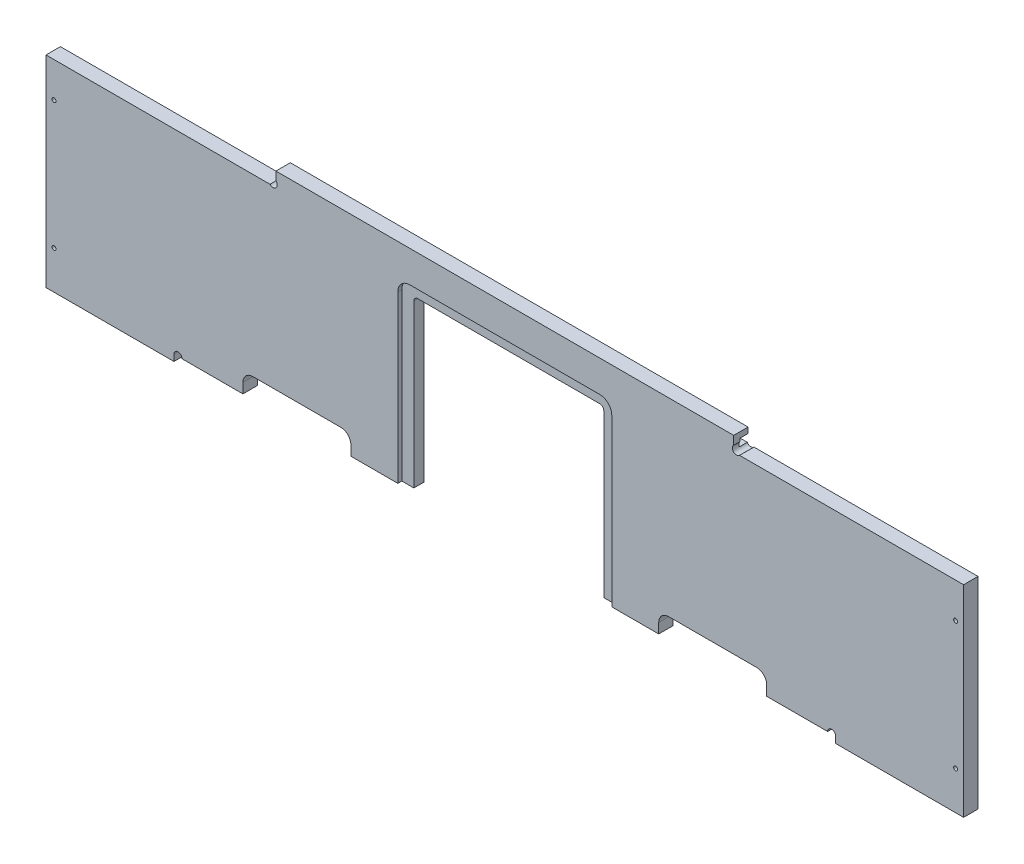
SolidWorks part; units mm, degrees
material "Pine"
ref_plane "Front Plane" through (0, 0, 0) normal (0, 0, 1) x (1, 0, 0)
ref_plane "Top Plane" through (0, 0, 0) normal (0, 1, 0) x (1, 0, 0)
ref_plane "Right Plane" through (0, 0, 0) normal (1, 0, 0) x (0, 0, -1)
sketch "Sketch1" plane through (0, 0, 0) normal (0, 0, 1) x (1, 0, 0)
  line L0 (-5300.6625, 1520.825) -> (-5451.475, 1520.825)
  line L1 (-5456.2375, 1384.3) -> (-5456.2375, 1516.0625)
  line L2 (-5557.8375, 1546.225) -> (-5194.3, 1546.225)
  line L3 (-5557.8375, 1539.875) -> (-5194.3, 1539.875)
  line L4 (-5297.4875, 1377.95) -> (-5454.65, 1377.95)
  line L5 (-5291.1375, 1384.3) -> (-5291.1375, 1516.0625)
  line L6 (-5300.6625, 1525.5875) -> (-5451.475, 1525.5875)
  line L7 (-5461, 1384.3) -> (-5461, 1516.0625)
  line L8 (-5297.4875, 1382.7125) -> (-5454.65, 1382.7125)
  line L9 (-5295.9, 1384.3) -> (-5295.9, 1516.0625)
  line L10 (-5740.4, 998.5375) -> (-5740.4, 1181.1)
  line L11 (-5740.4, 1181.1) -> (-5512.5938, 1181.1)
  line L12 (-5512.5938, 1181.1) -> (-5512.5938, 998.5375)
  line L13 (-5512.5938, 998.5375) -> (-5740.4, 998.5375)
  line L14 (-5258.5938, 1181.1) -> (-5486.4, 1181.1)
  line L15 (-5258.5938, 998.5375) -> (-5258.5938, 1181.1)
  line L16 (-5486.4, 998.5375) -> (-5258.5938, 998.5375)
  line L17 (-5486.4, 1181.1) -> (-5486.4, 998.5375)
  line L18 (-5740.4, 898.525) -> (-5011.7375, 898.525)
  line L19 (-5168.1062, 1384.3) -> (-5168.1062, 1392.2375)
  line L20 (-5176.0437, 1400.175) -> (-5245.8937, 1400.175)
  line L21 (-5253.8313, 1392.2375) -> (-5253.8313, 1384.3)
  line L22 (-5451.475, 1512.8875) -> (-5451.475, 1384.3)
  line L23 (-5303.8375, 1516.0625) -> (-5448.3, 1516.0625)
  line L24 (-5498.3062, 1384.3) -> (-5451.475, 1384.3)
  line L25 (-5253.8313, 1384.3) -> (-5300.6625, 1384.3)
  line L26 (-5584.0312, 1384.3) -> (-5740.4, 1384.3)
  line L27 (-5564.1875, 1536.7) -> (-5740.4, 1536.7)
  line L28 (-5740.4, 1357.3125) -> (-5740.4, 1206.5)
  line L29 (-5011.7375, 1357.3125) -> (-5740.4, 1357.3125)
  line L30 (-5011.7375, 1206.5) -> (-5011.7375, 1357.3125)
  line L31 (-5740.4, 1206.5) -> (-5011.7375, 1206.5)
  line L32 (-4765.675, 1549.4) -> (-4978.4, 1549.4)
  line L33 (-4765.675, 1397) -> (-4765.675, 1549.4)
  line L34 (-4978.4, 1397) -> (-4765.675, 1397)
  line L35 (-4978.4, 1549.4) -> (-4978.4, 1397)
  line L36 (-4765.675, 1371.6) -> (-4978.4, 1371.6)
  line L37 (-4765.675, 1219.2) -> (-4765.675, 1371.6)
  line L38 (-4978.4, 1219.2) -> (-4765.675, 1219.2)
  line L39 (-4978.4, 1371.6) -> (-4978.4, 1219.2)
  line L40 (-5284.7875, 803.275) -> (-5272.0875, 803.275)
  line L41 (-5187.95, 1536.7) -> (-5011.7375, 1536.7)
  line L42 (-5300.6625, 1384.3) -> (-5300.6625, 1512.8875)
  line L43 (-5740.4, 1536.7) -> (-5740.4, 1384.3)
  line L44 (-5557.8375, 1536.7) -> (-5557.8375, 1549.4)
  line L45 (-5557.8375, 1549.4) -> (-5194.3, 1549.4)
  line L46 (-5194.3, 1549.4) -> (-5194.3, 1536.7)
  line L47 (-5011.7375, 1536.7) -> (-5011.7375, 1384.3)
  line L48 (-5011.7375, 1384.3) -> (-5168.1062, 1384.3)
  line L49 (-5498.3062, 1384.3) -> (-5498.3062, 1392.2375)
  line L50 (-5506.2437, 1400.175) -> (-5576.0938, 1400.175)
  line L51 (-5584.0312, 1392.2375) -> (-5584.0312, 1384.3)
  line L52 (-5740.4, 660.4) -> (-5740.4, 898.525)
  line L53 (-5011.7375, 898.525) -> (-5011.7375, 660.4)
  line L54 (-5011.7375, 660.4) -> (-5740.4, 660.4)
  line L55 (-5291.1375, 803.275) -> (-5291.1375, 752.475)
  line L56 (-5265.7375, 752.475) -> (-5265.7375, 803.275)
  line L57 (-5284.7875, 752.475) -> (-5272.0875, 752.475)
  arc A0 (-5451.475, 1520.825) -> (-5456.2375, 1516.0625) centre (-5451.475, 1516.0625) ccw
  arc A1 (-5461, 1384.3) -> (-5454.65, 1377.95) centre (-5454.65, 1384.3) ccw
  arc A2 (-5297.4875, 1377.95) -> (-5291.1375, 1384.3) centre (-5297.4875, 1384.3) ccw
  circle A3 centre (-5037.9312, 1233.4875) radius 1.5875
  circle A4 centre (-5037.9312, 1328.7375) radius 1.5875
  circle A5 centre (-5714.2063, 1233.4875) radius 1.5875
  circle A6 centre (-5714.2063, 1328.7375) radius 1.5875
  circle A7 centre (-5018.0875, 1333.5) radius 1.5875
  circle A8 centre (-5018.0875, 1231.9) radius 1.5875
  circle A9 centre (-5734.05, 1231.9) radius 1.5875
  circle A10 centre (-5734.05, 1333.5) radius 1.5875
  circle A11 centre (-5734.05, 1511.3) radius 1.5875
  circle A12 centre (-5734.05, 1409.7) radius 1.5875
  circle A13 centre (-5018.0875, 1511.3) radius 1.5875
  circle A14 centre (-5018.0875, 1409.7) radius 1.5875
  arc A15 (-5557.8375, 1546.225) -> (-5557.8375, 1539.875) centre (-5557.8375, 1543.05) ccw
  arc A16 (-5194.3, 1539.875) -> (-5194.3, 1546.225) centre (-5194.3, 1543.05) ccw
  arc A17 (-5291.1375, 1516.0625) -> (-5300.6625, 1525.5875) centre (-5300.6625, 1516.0625) ccw
  arc A18 (-5451.475, 1525.5875) -> (-5461, 1516.0625) centre (-5451.475, 1516.0625) ccw
  arc A19 (-5456.2375, 1384.3) -> (-5454.65, 1382.7125) centre (-5454.65, 1384.3) ccw
  arc A20 (-5297.4875, 1382.7125) -> (-5295.9, 1384.3) centre (-5297.4875, 1384.3) ccw
  arc A21 (-5295.9, 1516.0625) -> (-5300.6625, 1520.825) centre (-5300.6625, 1516.0625) ccw
  circle A22 centre (-5702.3, 892.175) radius 1.5875
  circle A23 centre (-5734.05, 860.425) radius 1.5875
  circle A24 centre (-5474.8906, 892.175) radius 1.5875
  circle A25 centre (-5277.2469, 892.175) radius 1.5875
  circle A26 centre (-5049.8375, 892.175) radius 1.5875
  circle A27 centre (-5018.0875, 860.425) radius 1.5875
  circle A28 centre (-5296.6938, 1174.75) radius 1.5875
  circle A29 centre (-5448.3, 1174.75) radius 1.5875
  circle A30 centre (-5264.9437, 1155.7) radius 1.5875
  circle A31 centre (-5264.9437, 1023.9375) radius 1.5875
  circle A32 centre (-5518.9438, 1155.7) radius 1.5875
  circle A33 centre (-5518.9438, 1023.9375) radius 1.5875
  circle A34 centre (-5702.3, 1004.8875) radius 1.5875
  circle A35 centre (-5550.6937, 1004.8875) radius 1.5875
  arc A36 (-5576.0938, 1400.175) -> (-5584.0312, 1392.2375) centre (-5576.0938, 1392.2375) ccw
  arc A37 (-5168.1062, 1392.2375) -> (-5176.0437, 1400.175) centre (-5176.0437, 1392.2375) ccw
  arc A38 (-5245.8937, 1400.175) -> (-5253.8313, 1392.2375) centre (-5245.8937, 1392.2375) ccw
  arc A39 (-5448.3, 1516.0625) -> (-5451.475, 1512.8875) centre (-5448.3, 1512.8875) ccw
  arc A40 (-5284.7875, 803.275) -> (-5291.1375, 803.275) centre (-5287.9625, 803.275) ccw
  circle A41 centre (-5679.2812, 1026.3187) radius 1.5875
  circle A42 centre (-5679.2812, 1153.3187) radius 1.5875
  circle A43 centre (-5571.3313, 1153.3187) radius 1.5875
  circle A44 centre (-5571.3313, 1026.3187) radius 1.5875
  circle A45 centre (-5317.3312, 1153.3187) radius 1.5875
  circle A46 centre (-5317.3312, 1026.3187) radius 1.5875
  circle A47 centre (-5425.2812, 1026.3187) radius 1.5875
  circle A48 centre (-5425.2812, 1153.3187) radius 1.5875
  arc A49 (-5194.3, 1536.7) -> (-5187.95, 1536.7) centre (-5191.125, 1536.7) ccw
  arc A50 (-5564.1875, 1536.7) -> (-5557.8375, 1536.7) centre (-5561.0125, 1536.7) ccw
  arc A51 (-5300.6625, 1512.8875) -> (-5303.8375, 1516.0625) centre (-5303.8375, 1512.8875) ccw
  arc A52 (-5498.3062, 1392.2375) -> (-5506.2437, 1400.175) centre (-5506.2437, 1392.2375) ccw
  circle A53 centre (-5712.46, 784.225) radius 4.7625
  arc A54 (-5272.0875, 752.475) -> (-5265.7375, 752.475) centre (-5268.9125, 752.475) ccw
  arc A55 (-5291.1375, 752.475) -> (-5284.7875, 752.475) centre (-5287.9625, 752.475) ccw
  circle A56 centre (-5182.3938, 684.2125) radius 3.175
  circle A57 centre (-5239.5437, 684.2125) radius 3.175
  circle A58 centre (-5512.5938, 684.2125) radius 3.175
  circle A59 centre (-5569.7437, 684.2125) radius 3.175
  circle A60 centre (-5474.8906, 666.75) radius 1.5875
  circle A61 centre (-5277.2469, 666.75) radius 1.5875
  circle A62 centre (-5734.05, 698.5) radius 1.5875
  circle A63 centre (-5702.3, 666.75) radius 1.5875
  circle A64 centre (-5049.8375, 666.75) radius 1.5875
  circle A65 centre (-5018.0875, 698.5) radius 1.5875
  circle A66 centre (-5713.73, 835.025) radius 4.7625
  circle A67 centre (-5712.46, 819.785) radius 4.7625
  circle A68 centre (-5712.46, 802.005) radius 4.7625
  circle A69 centre (-5714.2063, 1314.45) radius 3.175
  circle A70 centre (-5037.9312, 1314.45) radius 3.175
  arc A71 (-5265.7375, 803.275) -> (-5272.0875, 803.275) centre (-5268.9125, 803.275) ccw
  ellipse E0 centre (-5371.3062, 1089.8188) end of major axis (-5277.6438, 1089.8188) minor radius 65.0875
  ellipse E1 centre (-5625.3062, 1089.8188) end of major axis (-5531.6438, 1089.8188) minor radius 65.0875
sketch "MainOutline" plane through (0, 0, 0) normal (0, 0, 1) x (1, 0, 0)
  line L0 (-5740.4, 1539.24) -> (-5740.4, 1384.3)
  line L1 (-5740.4, 1384.3) -> (-5584.0312, 1384.3)
  line L2 (-5584.0312, 1384.3) -> (-5584.0312, 1392.2375)
  line L3 (-5576.0938, 1400.175) -> (-5506.2437, 1400.175)
  line L4 (-5498.3062, 1392.2375) -> (-5498.3062, 1384.3)
  line L5 (-5498.3062, 1384.3) -> (-5451.475, 1384.3)
  line L6 (-5451.475, 1384.3) -> (-5451.475, 1512.8875)
  line L7 (-5448.3, 1516.0625) -> (-5303.8375, 1516.0625)
  line L8 (-5300.6625, 1512.8875) -> (-5300.6625, 1384.3)
  line L9 (-5300.6625, 1384.3) -> (-5253.8313, 1384.3)
  line L10 (-5253.8313, 1384.3) -> (-5253.8313, 1392.2375)
  line L11 (-5245.8937, 1400.175) -> (-5176.0437, 1400.175)
  line L12 (-5168.1062, 1392.2375) -> (-5168.1062, 1384.3)
  line L13 (-5168.1062, 1384.3) -> (-5011.7375, 1384.3)
  line L14 (-5011.7375, 1384.3) -> (-5011.7375, 1539.24)
  line L15 (-5011.7375, 1539.24) -> (-5194.3, 1539.24)
  line L16 (-5194.3, 1539.24) -> (-5194.3, 1550.67)
  line L17 (-5194.3, 1550.67) -> (-5557.8375, 1550.67)
  line L18 (-5557.8375, 1550.67) -> (-5557.8375, 1539.24)
  line L19 (-5557.8375, 1539.24) -> (-5740.4, 1539.24)
  arc A0 (-5584.0312, 1392.2375) -> (-5576.0938, 1400.175) centre (-5576.0938, 1392.2375) cw
  arc A1 (-5506.2437, 1400.175) -> (-5498.3062, 1392.2375) centre (-5506.2437, 1392.2375) cw
  arc A2 (-5451.475, 1512.8875) -> (-5448.3, 1516.0625) centre (-5448.3, 1512.8875) cw
  arc A3 (-5303.8375, 1516.0625) -> (-5300.6625, 1512.8875) centre (-5303.8375, 1512.8875) cw
  arc A4 (-5253.8313, 1392.2375) -> (-5245.8937, 1400.175) centre (-5245.8938, 1392.2375) cw
  arc A5 (-5176.0437, 1400.175) -> (-5168.1062, 1392.2375) centre (-5176.0437, 1392.2375) cw
  dimension "D1" = 11.43
  dimension "D2" = 166.37
extrude "Thickness_MainOutline" add sketch "MainOutline" against normal blind 11.43
sketch "CornerPocketRadius" plane through (0, 0, 0) normal (0, 0, 1) x (1, 0, 0)
  line L0 (-5557.8375, 1539.24) -> (-5560.0826, 1541.4851) construction
  line L1 (-5194.3, 1539.24) -> (-5192.0549, 1541.4851) construction
  line L2 (-5557.8375, 1539.24) -> (-5740.4, 1539.24) construction
  line L3 (-5011.7375, 1539.24) -> (-5194.3, 1539.24) construction
  circle A0 centre (-5560.0826, 1541.4851) radius 3.302
  circle A1 centre (-5192.0549, 1541.4851) radius 3.302
  dimension "D1" = 45
  dimension "D2" = 3.175
  dimension "D3" = 45
  dimension "D4" = 3.175
extrude "Cut-Extrude4" cut sketch "CornerPocketRadius" against normal up to surface (11.43 mm away) up to face at (-5376.0688, 1444.9285, -11.43)
sketch "PowerBoxFlange" plane through (0, 0, 0) normal (0, 0, 1) x (1, 0, 0)
  line L0 (-5297.4875, 1377.95) -> (-5454.65, 1377.95)
  line L1 (-5461, 1384.3) -> (-5461, 1516.0625)
  line L2 (-5451.475, 1525.5875) -> (-5300.6625, 1525.5875)
  line L3 (-5291.1375, 1516.0625) -> (-5291.1375, 1384.3)
  arc A0 (-5454.65, 1377.95) -> (-5461, 1384.3) centre (-5454.65, 1384.3) cw
  arc A1 (-5461, 1516.0625) -> (-5451.475, 1525.5875) centre (-5451.475, 1516.0625) cw
  arc A2 (-5300.6625, 1525.5875) -> (-5291.1375, 1516.0625) centre (-5300.6625, 1516.0625) cw
  arc A3 (-5291.1375, 1384.3) -> (-5297.4875, 1377.95) centre (-5297.4875, 1384.3) cw
extrude "FlangeDepth" cut sketch "PowerBoxFlange" against normal blind 3.175
sketch "ScrewHoles" plane through (0, 0, 0) normal (0, 0, 1) x (1, 0, 0)
  circle A0 centre (-5734.05, 1511.3) radius 1.5875
  circle A1 centre (-5734.05, 1409.7) radius 1.5875
  circle A2 centre (-5018.0875, 1409.7) radius 1.5875
  circle A3 centre (-5018.0875, 1511.3) radius 1.5875
extrude "Cut-Extrude2" cut sketch "ScrewHoles" against normal up to surface (11.43 mm away) up to face at (-5376.0688, 1451.8253, -11.43)
sketch "PlexChannel" plane through (0, 0, -11.43) normal (0, 0, -1) x (-1, 0, 0)
  line L0 (5557.8375, 1539.875) -> (5557.8375, 1546.225)
  line L1 (5557.8375, 1546.225) -> (5194.3, 1546.225)
  line L2 (5194.3, 1546.225) -> (5194.3, 1539.875)
  line L3 (5194.3, 1539.875) -> (5557.8375, 1539.875)
extrude "PlexChannel_Depth" cut sketch "PlexChannel" against normal blind 6.35
sketch "Sketch7" plane through (0, 0, 0) normal (0, 0, 1) x (1, 0, 0)
  line L0 (-5740.4, 1384.3) -> (-5740.4, 1379.22)
  line L1 (-5740.4, 1379.22) -> (-5638.8, 1379.22)
  line L2 (-5740.4, 1384.3) -> (-5584.0312, 1384.3) construction
  line L3 (-5638.8, 1384.3) -> (-5740.4, 1384.3)
  line L4 (-5638.8, 1379.22) -> (-5638.8, 1384.3)
  line L5 (-5011.7375, 1384.3) -> (-5011.7375, 1379.22)
  line L6 (-5011.7375, 1379.22) -> (-5113.3375, 1379.22)
  line L7 (-5113.3375, 1384.3) -> (-5011.7375, 1384.3)
  line L8 (-5168.1062, 1384.3) -> (-5011.7375, 1384.3) construction
  line L9 (-5113.3375, 1384.3) -> (-5113.3375, 1379.22)
  dimension "D1" = 5.08
  dimension "D2" = 101.6
  dimension "D3" = 101.6
extrude "Extrude2" add sketch "Sketch7" against normal up to surface (11.43 mm away) up to face at (-5376.0688, 1443.9942, -11.43)
sketch "Sketch8" plane through (0, 0, 0) normal (0, 0, 1) x (1, 0, 0)
  line L0 (-5638.8, 1384.3) -> (-5632.45, 1384.3) construction
  line L1 (-5638.8, 1384.3) -> (-5584.0312, 1384.3) construction
  line L2 (-5113.3375, 1384.3) -> (-5119.6875, 1384.3) construction
  line L3 (-5168.1062, 1384.3) -> (-5113.3375, 1384.3) construction
  circle A0 centre (-5635.625, 1384.3) radius 3.175
  circle A1 centre (-5116.5125, 1384.3) radius 3.175
extrude "Cut-Extrude5" cut sketch "Sketch8" against normal up to surface (11.43 mm away) up to face at (-5376.0688, 1435.3576, -11.43)
